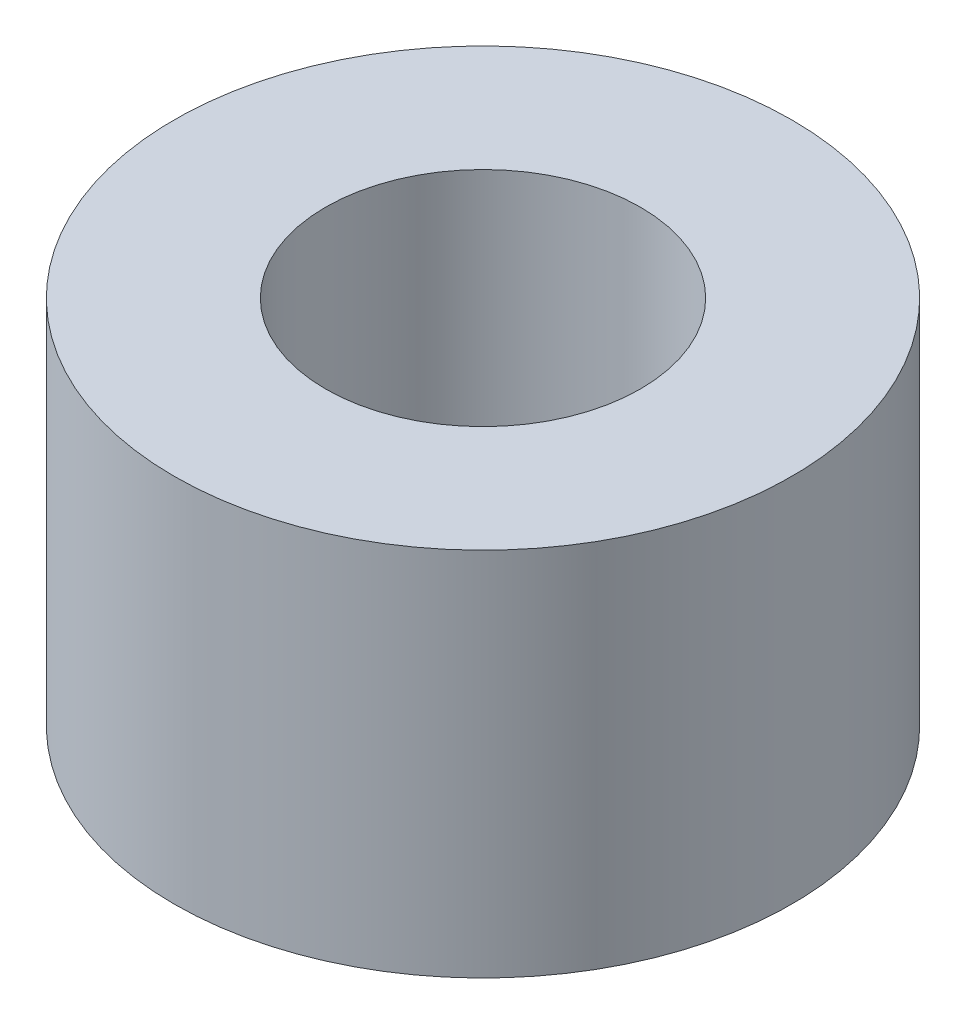
SolidWorks part; units mm, degrees
ref_plane "Alzado" through (0, 0, 0) normal (0, 0, 1) x (1, 0, 0)
ref_plane "Planta" through (0, 0, 0) normal (0, 1, 0) x (1, 0, 0)
ref_plane "Vista lateral" through (0, 0, 0) normal (1, 0, 0) x (0, 0, -1)
sketch "Croquis1" plane through (0, 0, 0) normal (0, 1, 0) x (1, 0, 0)
  circle A0 centre (0, 0) radius 2.55
  circle A1 centre (0, 0) radius 5
  point P3 (0, 0)
  dimension "D1" = 5.1
  dimension "D2" = 10
extrude "Saliente-Extruir1" add sketch "Croquis1" along normal blind 6
